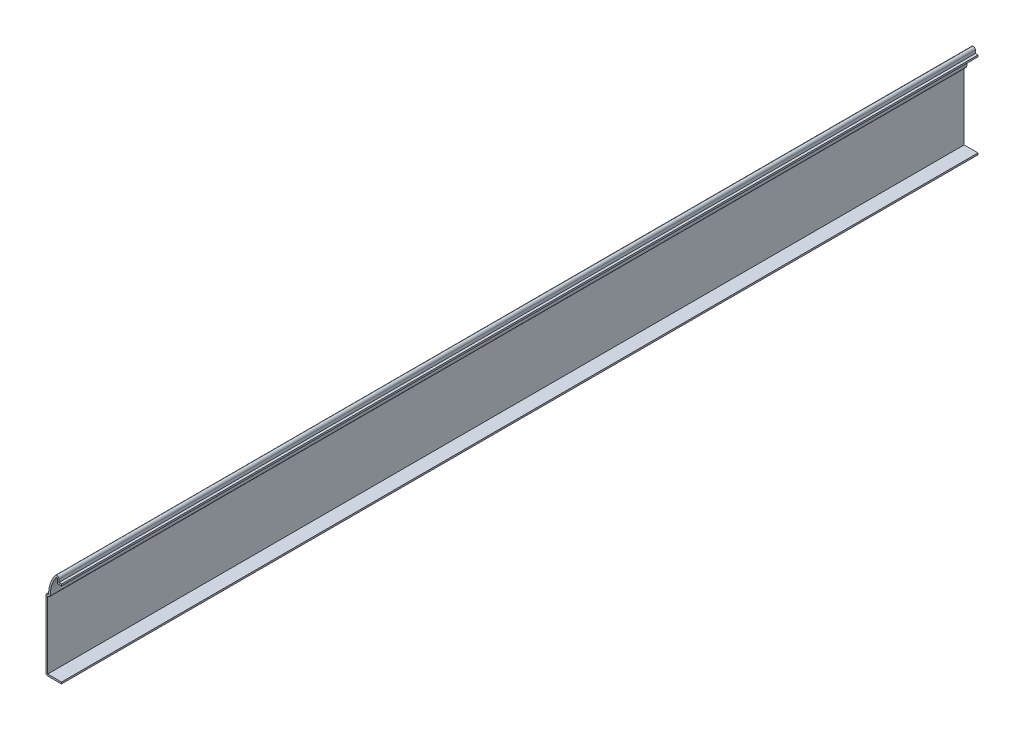
SolidWorks part; units mm, degrees
ref_plane "Front Plane" through (0, 0, 0) normal (0, 0, 1) x (1, 0, 0)
ref_plane "Top Plane" through (0, 0, 0) normal (0, 1, 0) x (1, 0, 0)
ref_plane "Right Plane" through (0, 0, 0) normal (1, 0, 0) x (0, 0, -1)
sketch "Sketch1" plane through (0, 0, 0) normal (0, 0, 1) x (1, 0, 0)
  line L0 (0, 0) -> (-9.525, 0)
  line L1 (-9.525, 0) -> (-9.525, 43.6562)
  line L2 (-9.525, 43.6562) -> (-7.9375, 43.6562)
  line L3 (-1.5875, 55.0863) -> (-1.5875, 53.1813)
  line L4 (-1.5875, 53.1813) -> (0, 53.1813)
  arc A0 (-7.9375, 43.6562) -> (-3.8735, 55.8483) centre (12.3825, 43.6562) cw
  arc A1 (-3.8735, 55.8483) -> (-1.5875, 55.0863) centre (-2.8575, 55.0863) cw
  point P9 (0, 0)
  dimension "D8" = 56.3562
  dimension "D9" = 1.27
  dimension "D1" = 9.525
  dimension "D2" = 43.6562
  dimension "D3" = 1.5875
  dimension "D4" = 1.5875
  dimension "D5" = 12.7
  dimension "D6" = 3.175
  dimension "D7" = 6.35
extrude "Extrude-Thin1" add sketch "Sketch1" against normal blind 563.5625 thin
fillet "Fillet1" radius 1.016 4 edges at (-9.525, 0, -281.7812) (-9.525, 43.6562, -281.7812) (-6.8947, 42.6402, -281.7812) (-2.6035, 52.1653, -281.7812)
